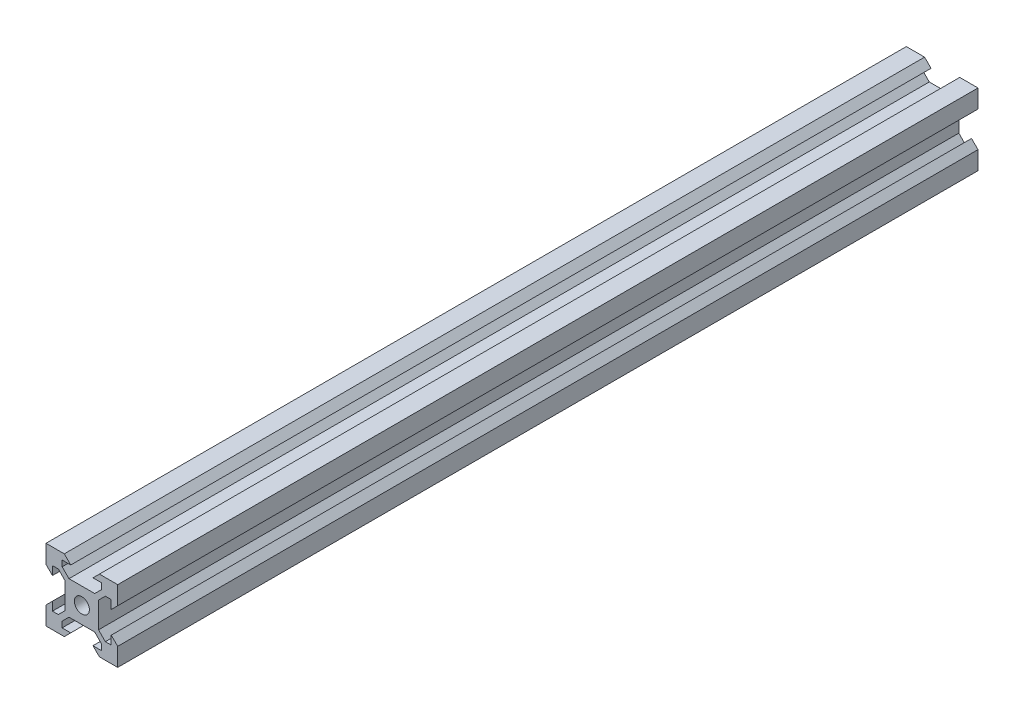
SolidWorks part; units mm, degrees
material "6063-T5"
ref_plane "Front Plane" through (0, 0, 0) normal (0, 0, 1) x (1, 0, 0)
ref_plane "Top Plane" through (0, 0, 0) normal (0, 1, 0) x (1, 0, 0)
ref_plane "Right Plane" through (0, 0, 0) normal (1, 0, 0) x (0, 0, -1)
sketch "Sketch1" plane through (0, 0, 0) normal (0, 0, 1) x (1, 0, 0)
  line L0 (3.59, 4.6507) -> (-3.59, 4.6507)
  line L5 (-10, -10) -> (10, -10)
  line L6 (-10, -10) -> (-10, 10)
  line L7 (-10, 10) -> (10, 10)
  line L8 (10, -10) -> (10, 10)
  line L9 (-10, -10) -> (10, 10) construction
  line L10 (-10, 10) -> (10, -10) construction
  line L11 (0, 10) -> (0, -10) construction
  line L12 (10, 0) -> (-10, 0) construction
  line L13 (-3.59, 4.6507) -> (-5.4993, 6.56)
  line L14 (-5.4993, 6.56) -> (-5.4993, 8.2)
  line L15 (3.59, 4.6507) -> (5.4993, 6.56)
  line L16 (5.4993, 6.56) -> (5.4993, 8.2)
  line L17 (5.4993, 8.2) -> (3.1, 8.2)
  line L18 (3.1, 8.2) -> (4.9, 10)
  line L19 (-5.4993, 8.2) -> (-3.1, 8.2)
  line L20 (-3.1, 8.2) -> (-4.9, 10)
  line L21 (3.1, -8.2) -> (4.9, -10)
  line L22 (5.4993, -8.2) -> (3.1, -8.2)
  line L23 (5.4993, -6.56) -> (5.4993, -8.2)
  line L24 (3.59, -4.6507) -> (5.4993, -6.56)
  line L25 (3.59, -4.6507) -> (-3.59, -4.6507)
  line L26 (-3.59, -4.6507) -> (-5.4993, -6.56)
  line L27 (-5.4993, -6.56) -> (-5.4993, -8.2)
  line L28 (-5.4993, -8.2) -> (-3.1, -8.2)
  line L29 (-3.1, -8.2) -> (-4.9, -10)
  line L30 (8.2, 3.1) -> (10, 4.9)
  line L31 (8.2, 3.1) -> (8.2, 5.4993)
  line L32 (8.2, 5.4993) -> (6.56, 5.4993)
  line L33 (4.6507, 3.59) -> (6.56, 5.4993)
  line L34 (4.6507, 3.59) -> (4.6507, -3.59)
  line L35 (4.6507, -3.59) -> (6.56, -5.4993)
  line L36 (8.2, -5.4993) -> (6.56, -5.4993)
  line L37 (8.2, -3.1) -> (8.2, -5.4993)
  line L38 (8.2, -3.1) -> (10, -4.9)
  line L39 (-8.2, -3.1) -> (-10, -4.9)
  line L40 (-8.2, -3.1) -> (-8.2, -5.4993)
  line L41 (-8.2, -5.4993) -> (-6.56, -5.4993)
  line L42 (-4.6507, -3.59) -> (-6.56, -5.4993)
  line L43 (-4.6507, 3.59) -> (-4.6507, -3.59)
  line L44 (-4.6507, 3.59) -> (-6.56, 5.4993)
  line L45 (-8.2, 5.4993) -> (-6.56, 5.4993)
  line L46 (-8.2, 3.1) -> (-8.2, 5.4993)
  line L47 (-8.2, 3.1) -> (-10, 4.9)
  line L48 (4.9, 10) -> (-4.9, 10)
  line L49 (-10, 4.9) -> (-10, -4.9)
  line L50 (10, -4.9) -> (10, 4.9)
  line L51 (4.9, -10) -> (-4.9, -10)
  circle A1 centre (0, 0) radius 2.1
  point P11 (0, 4.6507)
  point P35 (4.6507, 0)
  dimension "D1" = 4.2
  dimension "D2" = 20
  dimension "D3" = 20
  dimension "D4" = 0.75
  dimension "D5" = 3.59
  dimension "D6" = 3.1
  dimension "D7" = 1.8
  dimension "D8" = 1.64
  dimension "D9" = 3.59
  dimension "D10" = 1.64
  dimension "D11" = 1.8
  dimension "D12" = 45
  dimension "D13" = 0.75
  dimension "D14" = 3.1
extrude "Boss-Extrude1" add sketch "Sketch1" along normal mid plane 240 contours L6 L5 L8 L7 | A1 | L50 L30 L31 L32 L33 L34 L35 L36 L37 L38 | L48 L20 L19 L14 L13 L0 L15 L16 L17 L18 | L49 L39 L40 L41 L42 L43 L44 L45 L46 L47 | L51 L29 L28 L27 L26 L25 L24 L23 L22 L21
